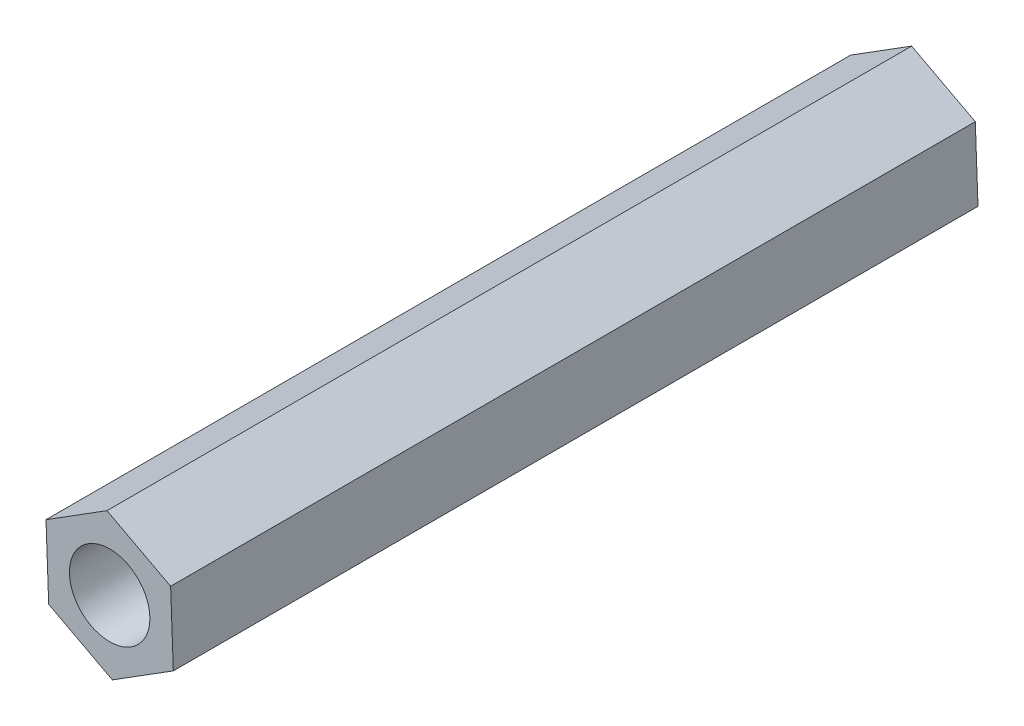
SolidWorks part; units mm, degrees
ref_plane "前视基准面" through (0, 0, 0) normal (0, 0, 1) x (1, 0, 0)
ref_plane "上视基准面" through (0, 0, 0) normal (0, 1, 0) x (1, 0, 0)
ref_plane "右视基准面" through (0, 0, 0) normal (1, 0, 0) x (0, 0, -1)
sketch "草图1" plane through (0, 0, 0) normal (0, 0, 1) x (1, 0, 0)
  line L1 (2.2732, 1.4283) -> (-0.1003, 2.6828)
  line L2 (-0.1003, 2.6828) -> (-2.3735, 1.2545)
  line L3 (-2.3735, 1.2545) -> (-2.2732, -1.4283)
  line L4 (-2.2732, -1.4283) -> (0.1003, -2.6828)
  line L5 (0.1003, -2.6828) -> (2.3735, -1.2545)
  line L6 (2.3735, -1.2545) -> (2.2732, 1.4283)
  circle A0 centre (0, 0) radius 2.325 construction
  circle A1 centre (0, 0) radius 1.5
extrude "凸台-拉伸1" add sketch "草图1" along normal blind 30
